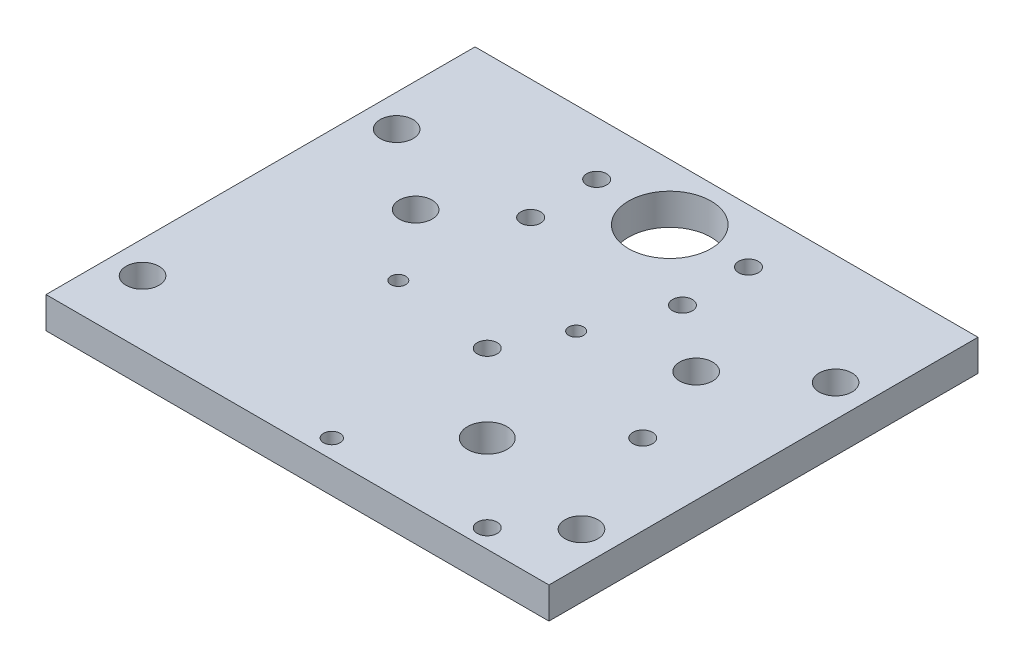
SolidWorks part; units mm, degrees
ref_plane "Front Plane" through (0, 0, 0) normal (0, 0, 1) x (1, 0, 0)
ref_plane "Top Plane" through (0, 0, 0) normal (0, 1, 0) x (1, 0, 0)
ref_plane "Right Plane" through (0, 0, 0) normal (1, 0, 0) x (0, 0, -1)
sketch "Sketch1" plane through (0, 0, 0) normal (0, 1, 0) x (1, 0, 0)
  line L1 (-76.2, -65) -> (76.2, -65)
  line L2 (-76.2, -65) -> (-76.2, 65)
  line L3 (-76.2, 65) -> (76.2, 65)
  line L4 (76.2, -65) -> (76.2, 65)
  line L5 (-76.2, -65) -> (76.2, 65) construction
  line L6 (-76.2, 65) -> (76.2, -65) construction
  point P0 (0, 0)
  dimension "D1" = 130
  dimension "D2" = 152.4
extrude "Boss-Extrude1" add sketch "Sketch1" along normal blind 9.5
sketch "Sketch2" plane through (0, 0, 0) normal (0, -1, 0) x (-1, 0, 0)
  circle A0 centre (-4.75, -59.35) radius 2.5
  circle A1 centre (-51.85, -59.35) radius 3
  circle A2 centre (-4.75, -12.25) radius 3
  circle A3 centre (-51.85, -12.25) radius 3
  dimension "D1" = 5
extrude "Cut-Extrude1" cut sketch "Sketch2" against normal blind 10
sketch "Sketch3" plane through (0, 9.5, 0) normal (0, 1, 0) x (1, 0, 0)
  circle A0 centre (28.3, -35.8) radius 6
  dimension "D1" = 12
extrude "Cut-Extrude2" cut sketch "Sketch3" against normal blind 10 contours A0
sketch "Sketch4" plane through (0, 9.5, 0) normal (0, 1, 0) x (1, 0, 0)
  circle A0 centre (-26.5341, -7.922) radius 2.25
  circle A1 centre (13.7219, 5.7053) radius 2.25
  circle A2 centre (0, 47.8) radius 12.5
extrude "Cut-Extrude3" cut sketch "Sketch4" against normal through all
sketch "Sketch5" plane through (0, 9.5, 0) normal (0, 1, 0) x (1, 0, 0)
  line L0 (0, 47.8) -> (0, 38.65) construction
  line L2 (23, 28.65) -> (-23, 28.65) construction
  line L3 (23, 28.65) -> (23, 48.65) construction
  line L4 (23, 48.65) -> (-23, 48.65) construction
  line L5 (-23, 28.65) -> (-23, 48.65) construction
  line L6 (23, 28.65) -> (-23, 48.65) construction
  line L7 (23, 48.65) -> (-23, 28.65) construction
  circle A0 centre (23, 28.65) radius 3
  circle A1 centre (-23, 28.65) radius 3
  circle A2 centre (23, 48.65) radius 3
  circle A3 centre (-23, 48.65) radius 3
  dimension "D1" = 46
  dimension "D2" = 20
  dimension "D3" = 19.15
extrude "Cut-Extrude4" cut sketch "Sketch5" against normal through all
sketch "Sketch6" plane through (0, 9.5, 0) normal (0, 1, 0) x (1, 0, 0)
  line L0 (-66.5, 65) -> (-66.5, -65) construction
  line L1 (76.2, 65) -> (-76.2, 65) construction
  line L2 (-76.2, -65) -> (76.2, -65) construction
  line L3 (-76.2, 65) -> (-76.2, -65) construction
  line L4 (0, 0) -> (0, 23.2681) construction
  line L5 (66.5, 65) -> (66.5, -65) construction
  line L6 (66.5, 13.3) -> (-66.5, 13.3) construction
  line L7 (76.2, -65) -> (76.2, 65) construction
  circle A0 centre (-66.5, 31.55) radius 5
  circle A1 centre (-66.5, -45.45) radius 5
  circle A2 centre (66.5, -45.45) radius 5
  circle A3 centre (66.5, 31.55) radius 5
  circle A4 centre (-42.5, 13.3) radius 5
  circle A5 centre (42.5, 13.3) radius 5
  dimension "D2" = 33.45
  dimension "D4" = 10
  dimension "D5" = 10
  dimension "D7" = 10
  dimension "D10" = 10
  dimension "D1" = 9.7
  dimension "D3" = 110.45
  dimension "D6" = 51.7
  dimension "D8" = 33.7
  dimension "D9" = 33.7
extrude "Cut-Extrude5" cut sketch "Sketch6" against normal through all
